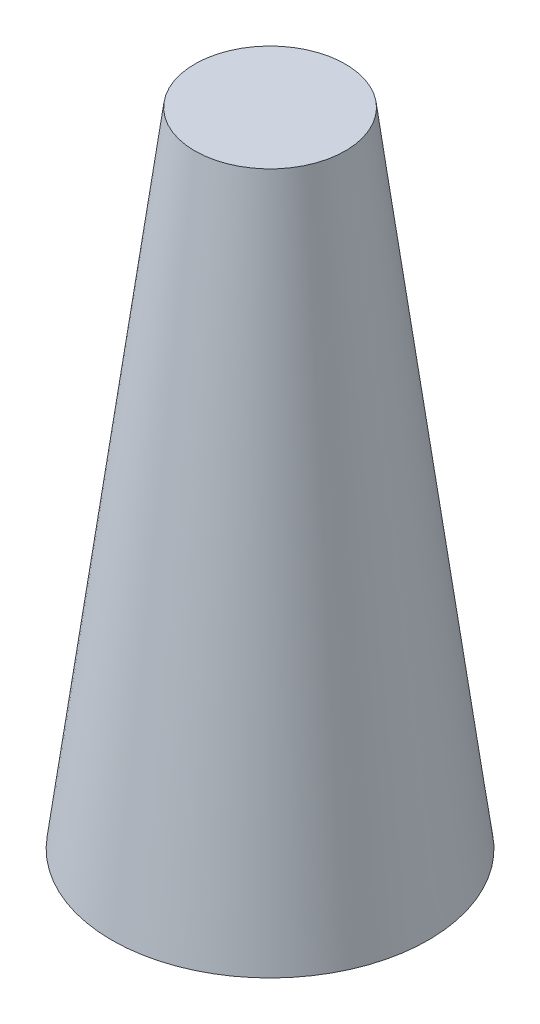
SolidWorks part; units mm, degrees
ref_plane "Front Plane" through (0, 0, 0) normal (0, 0, 1) x (1, 0, 0)
ref_plane "Top Plane" through (0, 0, 0) normal (0, 1, 0) x (1, 0, 0)
ref_plane "Right Plane" through (0, 0, 0) normal (1, 0, 0) x (0, 0, -1)
sketch "Sketch1" plane through (0, 0, 0) normal (0, 1, 0) x (1, 0, 0)
  circle A0 centre (0, 0) radius 126
  dimension "D1" = 252
ref_plane "Plane1" through (0, 510.8, 0) normal (0, 1, 0) x (1, 0, 0)
sketch "Sketch2" plane through (0, 510.8, 0) normal (0, 1, 0) x (1, 0, 0)
  circle A0 centre (0, 0) radius 59.9
  dimension "D1" = 119.8
loft "Loft1" add profiles "Sketch1", "Sketch2"
